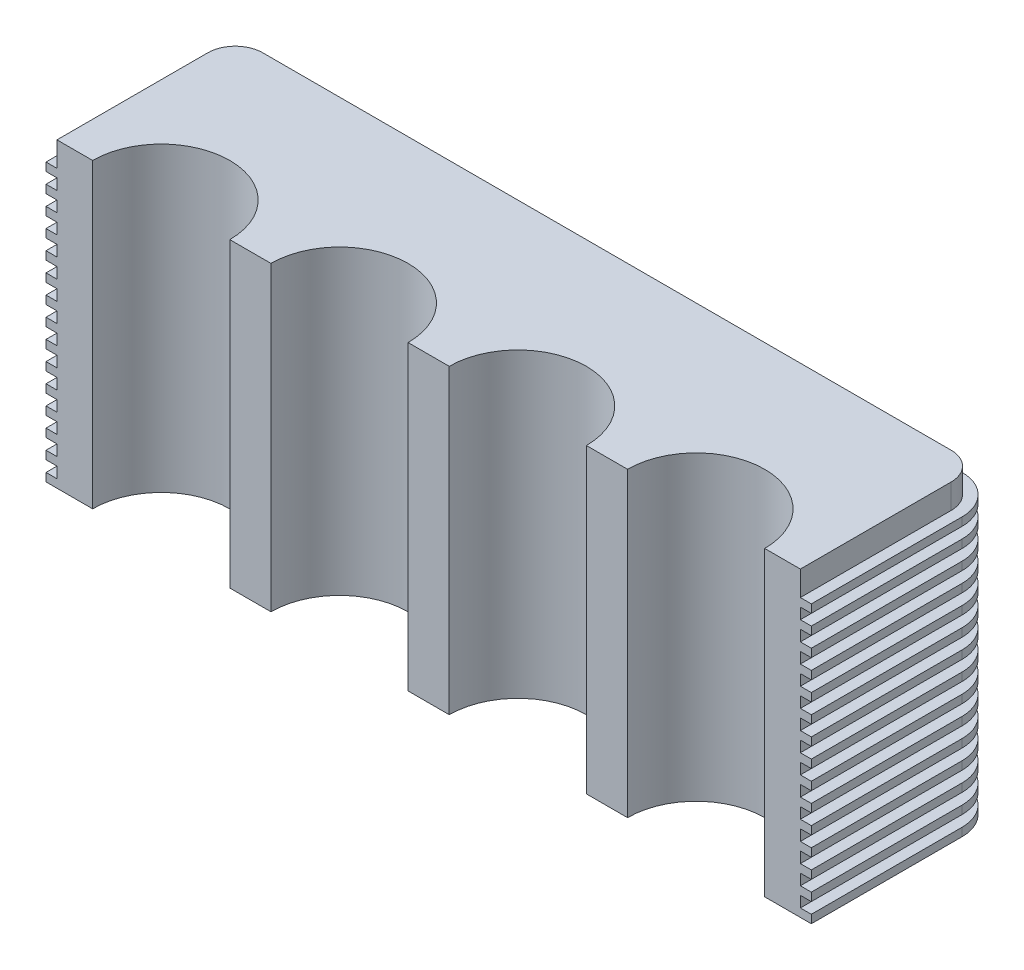
SolidWorks part; units mm, degrees
ref_plane "Front Plane" through (0, 0, 0) normal (0, 0, 1) x (1, 0, 0)
ref_plane "Top Plane" through (0, 0, 0) normal (0, 1, 0) x (1, 0, 0)
ref_plane "Right Plane" through (0, 0, 0) normal (1, 0, 0) x (0, 0, -1)
sketch "Sketch1" plane through (0, 0, 0) normal (0, 1, 0) x (1, 0, 0)
  line L0 (135.5, 65) -> (135.5, 0) construction
  line L1 (63, 0) -> (78, 0)
  line L2 (0, 0) -> (0, 55)
  line L3 (10, 65) -> (261, 65)
  line L4 (271, 0) -> (271, 55)
  line L5 (258, 0) -> (271, 0)
  line L6 (193, 0) -> (208, 0)
  line L7 (128, 0) -> (143, 0)
  line L8 (0, 0) -> (13, 0)
  arc A0 (261, 65) -> (271, 55) centre (261, 55) cw
  arc A1 (0, 55) -> (10, 65) centre (10, 55) cw
  arc A2 (258, 0) -> (208, 0) centre (233, 0) ccw
  arc A3 (193, 0) -> (143, 0) centre (168, 0) ccw
  arc A4 (13, 0) -> (63, 0) centre (38, 0) cw
  arc A5 (78, 0) -> (128, 0) centre (103, 0) cw
  point P7 (271, 65)
  point P10 (0, 65)
  dimension "D3" = 10
  dimension "D4" = 50
  dimension "D6" = 50
  dimension "D1" = 65
  dimension "D2" = 271
  dimension "D5" = 13
  dimension "D7" = 15
extrude "Boss-Extrude1" add sketch "Sketch1" along normal blind 110
sketch "Sketch4" plane through (0, 0, 0) normal (0, -1, 0) x (1, 0, 0)
  line L0 (-4, 0) -> (-4, -55)
  line L1 (10, -69) -> (261, -69)
  line L2 (275, -55) -> (275, 0)
  line L3 (0, 0) -> (-4, 0)
  line L4 (271, 0) -> (275, 0)
  line L8 (13, 0) -> (0, 0)
  line L9 (0, 0) -> (0, -55)
  line L10 (10, -65) -> (261, -65)
  line L11 (271, -55) -> (271, 0)
  line L12 (271, 0) -> (258, 0)
  line L13 (208, 0) -> (193, 0)
  line L14 (143, 0) -> (128, 0)
  line L15 (78, 0) -> (63, 0)
  line L17 (0, 0) -> (0, -55)
  line L18 (10, -65) -> (261, -65)
  line L19 (271, -55) -> (271, 0)
  arc A0 (-4, -55) -> (10, -69) centre (10, -55) ccw
  arc A1 (261, -69) -> (275, -55) centre (261, -55) ccw
  arc A6 (0, -55) -> (10, -65) centre (10, -55) ccw
  arc A7 (261, -65) -> (271, -55) centre (261, -55) ccw
  arc A8 (208, 0) -> (258, 0) centre (233, 0) ccw
  arc A9 (143, 0) -> (193, 0) centre (168, 0) ccw
  arc A10 (78, 0) -> (128, 0) centre (103, 0) ccw
  arc A11 (13, 0) -> (63, 0) centre (38, 0) ccw
  arc A12 (0, -55) -> (10, -65) centre (10, -55) ccw
  arc A13 (261, -65) -> (271, -55) centre (261, -55) ccw
  dimension "D1" = 0
  dimension "D2" = 4
extrude "Boss-Extrude2" add sketch "Sketch4" against normal blind 3
pattern_linear "LPattern1" count 15 spacing 7 along (0, 1, 0) of "Boss-Extrude2"
